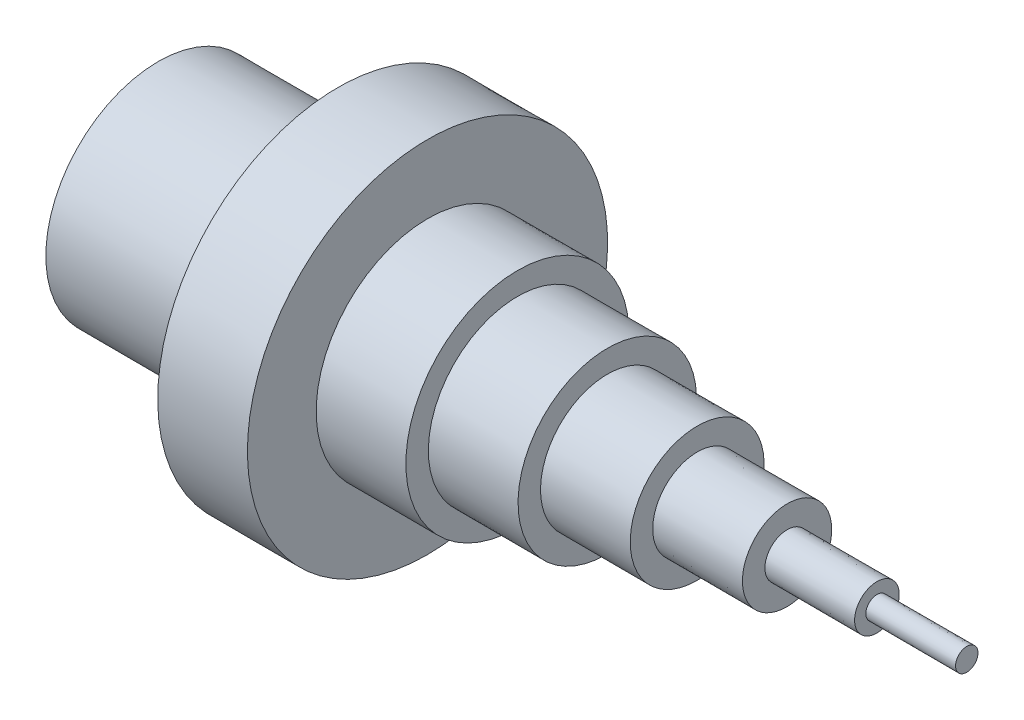
SolidWorks part; units mm, degrees
ref_plane "Front" through (0, 0, 0) normal (0, 0, 1) x (1, 0, 0)
ref_plane "Top" through (0, 0, 0) normal (0, 1, 0) x (1, 0, 0)
ref_plane "Right" through (0, 0, 0) normal (1, 0, 0) x (0, 0, -1)
sketch "Sketch1" plane through (0, 0, 0) normal (0, 0, 1) x (1, 0, 0)
  line L0 (0, 0) -> (0, 25)
  line L1 (0, 25) -> (40, 25)
  line L2 (40, 25) -> (40, 40)
  line L3 (40, 40) -> (60, 40)
  line L4 (60, 40) -> (60, 24.7196)
  line L5 (60, 24.7196) -> (80, 24.7196)
  line L6 (80, 24.7196) -> (80, 19.7196)
  line L7 (80, 19.7196) -> (100, 19.7196)
  line L8 (100, 19.7196) -> (100, 14.7196)
  line L9 (100, 14.7196) -> (120, 14.7196)
  line L10 (120, 14.7196) -> (120, 9.7196)
  line L11 (120, 9.7196) -> (140, 9.7196)
  line L12 (140, 9.7196) -> (140, 4.7196)
  line L13 (140, 4.7196) -> (160, 4.7196)
  line L14 (160, 4.7196) -> (160, 2.2196)
  line L15 (160, 2.2196) -> (180, 2.2196)
  line L16 (180, 2.2196) -> (179.9998, -0.2804)
  line L17 (-27.7929, 0) -> (207.645, 0) construction
  line L18 (0, 0) -> (179.9998, -0.2804)
  dimension "D1" = 180
  dimension "D2" = 40
  dimension "D3" = 20
  dimension "D4" = 20
  dimension "D5" = 20
  dimension "D6" = 20
  dimension "D7" = 20
  dimension "D8" = 20
  dimension "D9" = 20
  dimension "D10" = 15
  dimension "D11" = 5
  dimension "D12" = 2.5
  dimension "D13" = 2.5
  dimension "D14" = 5
  dimension "D15" = 5
  dimension "D16" = 5
  dimension "D17" = 40
revolve "Revolve1" add sketch "Sketch1" angle 360 about L18
